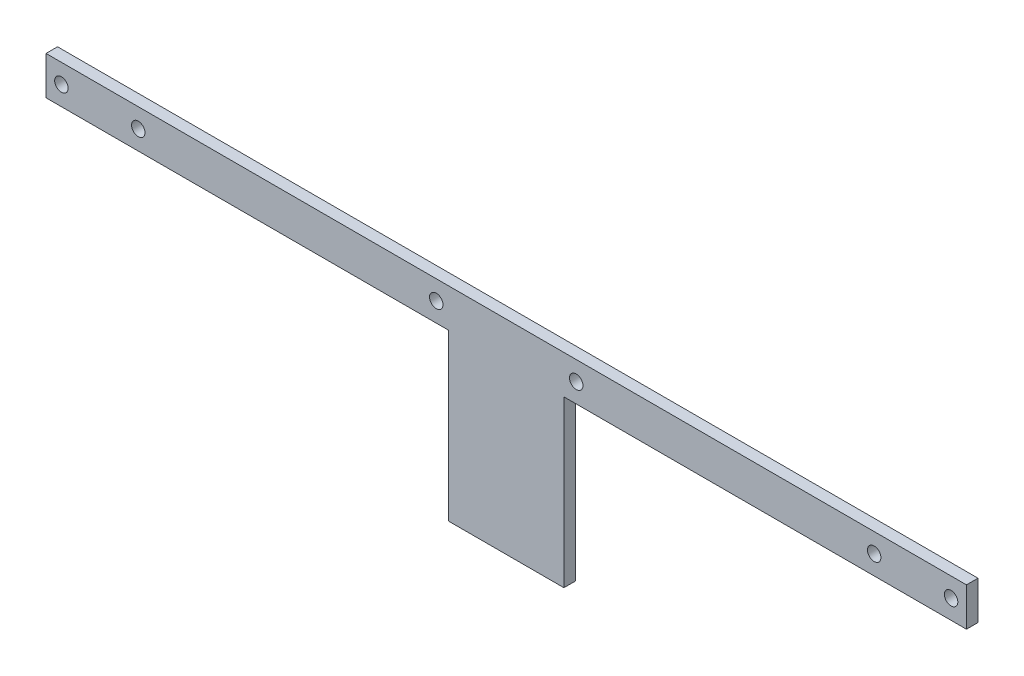
SolidWorks part; units mm, degrees
ref_plane "Front Plane" through (0, 0, 0) normal (0, 0, 1) x (1, 0, 0)
ref_plane "Top Plane" through (0, 0, 0) normal (0, 1, 0) x (1, 0, 0)
ref_plane "Right Plane" through (0, 0, 0) normal (1, 0, 0) x (0, 0, -1)
sketch "Sketch1" plane through (0, 0, 0) normal (0, 0, 1) x (1, 0, 0)
  line L0 (0, 5) -> (4, 5) construction
  line L1 (0, 0) -> (239.4, 0) construction
  line L2 (0, 0) -> (0, 10)
  line L3 (0, 10) -> (239.4, 10)
  line L4 (239.4, 0) -> (239.4, 10)
  line L5 (4, 5) -> (24, 5) construction
  line L6 (239.4, 5) -> (235.4, 5) construction
  line L7 (235.4, 5) -> (215.4, 5) construction
  line L8 (119.7, 10) -> (119.7, 0) construction
  line L9 (104.7, -43) -> (134.7, -43)
  line L10 (134.7, 0) -> (134.7, -43)
  line L11 (101.5, 5) -> (119.7, 5) construction
  line L12 (119.7, 5) -> (137.9, 5) construction
  line L13 (104.7, -43) -> (104.7, 0)
  line L14 (119.7, 0) -> (119.7, -43) construction
  line L15 (104.7, 0) -> (0, 0)
  line L16 (134.7, 0) -> (239.4, 0)
  circle A0 centre (4, 5) radius 1.75
  circle A1 centre (24, 5) radius 1.75
  circle A2 centre (235.4, 5) radius 1.75
  circle A3 centre (215.4, 5) radius 1.75
  circle A4 centre (101.5, 5) radius 1.75
  circle A5 centre (137.9, 5) radius 1.75
  point P23 (119.7, 5)
  dimension "D3" = 3.5
  dimension "D4" = 3.5
  dimension "D8" = 3.5
  dimension "D9" = 3.5
  dimension "D11" = 3.5
  dimension "D12" = 3.5
  dimension "D1" = 239.4
  dimension "D2" = 10
  dimension "D5" = 20
  dimension "D6" = 4
  dimension "D10" = 20
  dimension "D13" = 18.2
  dimension "D14" = 30
  dimension "D15" = 43
extrude "Boss-Extrude1" add sketch "Sketch1" along normal blind 3
equation "\"8.6.5mm\"=8.4"
